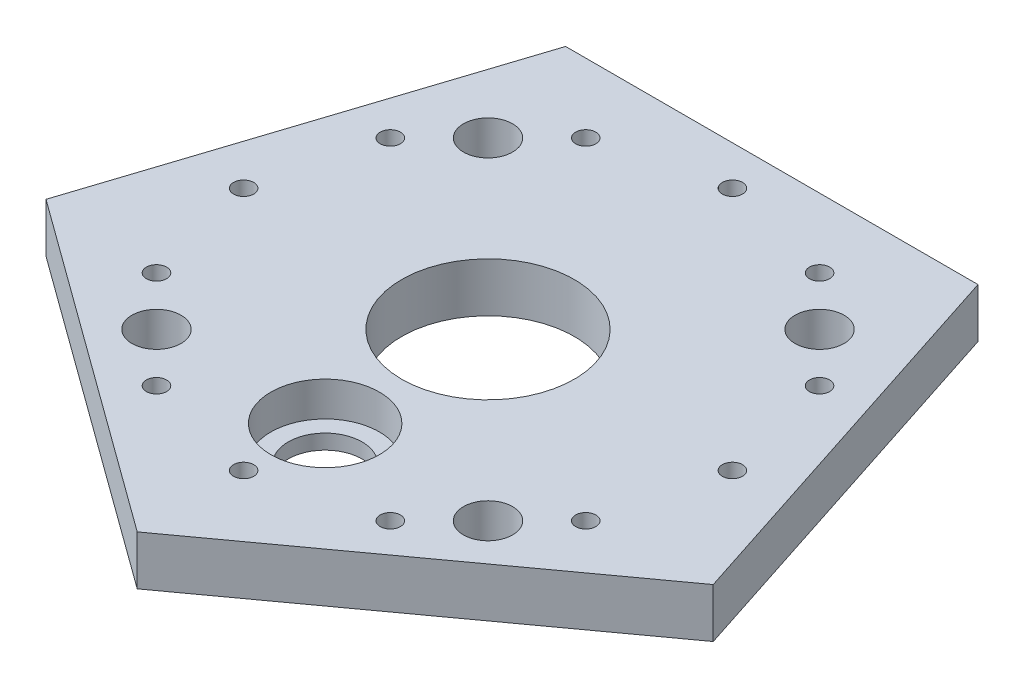
SolidWorks part; units mm, degrees
ref_plane "Front Plane" through (0, 0, 0) normal (0, 0, 1) x (1, 0, 0)
ref_plane "Top Plane" through (0, 0, 0) normal (0, 1, 0) x (1, 0, 0)
ref_plane "Right Plane" through (0, 0, 0) normal (1, 0, 0) x (0, 0, -1)
sketch "Sketch1" plane through (0, 0, 0) normal (0, 1, 0) x (1, 0, 0)
  line L101 (0, -71.0739) -> (67.5953, -21.963)
  line L102 (67.5953, -21.963) -> (41.7762, 57.5)
  line L103 (41.7762, 57.5) -> (-41.7762, 57.5)
  line L104 (-41.7762, 57.5) -> (-67.5953, -21.963)
  line L105 (-67.5953, -21.963) -> (0, -71.0739)
  circle A1 centre (0, 0) radius 57.5 construction
  dimension "D1" = 115
extrude "Boss-Extrude1" add sketch "Sketch1" along normal blind 10
sketch "Sketch2" plane through (0, 10, 0) normal (0, 1, 0) x (1, 0, 0)
  circle A0 centre (0, -33) radius 11
  dimension "D2" = 22
  dimension "D1" = 33
extrude "Cut-Extrude1" cut sketch "Sketch2" against normal blind 7
sketch "Sketch3" plane through (0, 3, 0) normal (0, 1, 0) x (1, 0, 0)
  circle A0 centre (0, -33) radius 7.5
  dimension "D1" = 15
extrude "Cut-Extrude2" cut sketch "Sketch3" against normal through all
sketch "Sketch5" plane through (0, 10, 0) normal (0, 1, 0) x (1, 0, 0)
  line L0 (0, 0) -> (-33.5876, -33.5876) construction
  line L1 (0, 0) -> (0, -33) construction
  line L2 (-9.8995, 9.8995) -> (-43.4871, -23.6881) construction
  line L3 (9.8995, -9.8995) -> (-23.6881, -43.4871) construction
  circle A0 centre (-33.5876, -33.5876) radius 4.975
  circle A2 centre (-43.4871, -23.6881) radius 2.05
  circle A3 centre (-23.6881, -43.4871) radius 2.05
  dimension "D2" = 9.95
  dimension "D6" = 4.1
  dimension "D7" = 4.1
  dimension "D1" = 47.5
  dimension "D3" = 45
  dimension "D4" = 14
  dimension "D5" = 14
extrude "Cut-Extrude4" cut sketch "Sketch5" against normal through all
sketch "Sketch6" plane through (0, 10, 0) normal (0, 1, 0) x (1, 0, 0)
  circle A0 centre (0, -49.52) radius 2.05
  point P5 (0, 0)
  dimension "D2" = 4.1
  dimension "D1" = 49.52
extrude "Cut-Extrude5" cut sketch "Sketch6" against normal through all
pattern_circular "CirPattern1" count 4 over 360 about axis through (0, 0, 0) along (0, 1, 0) of "Cut-Extrude4", "Cut-Extrude5"
sketch "Sketch7" plane through (0, 10, 0) normal (0, 1, 0) x (1, 0, 0)
  circle A0 centre (0, 0) radius 17.5
  dimension "D1" = 35
extrude "Cut-Extrude6" cut sketch "Sketch7" against normal through all contours A0
